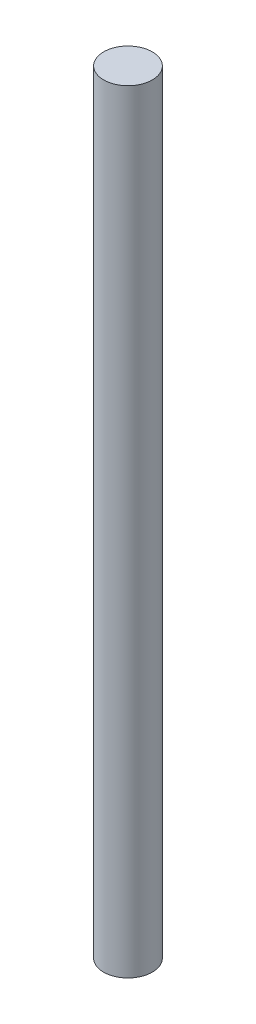
SolidWorks part; units mm, degrees
ref_plane "Front Plane" through (0, 0, 0) normal (0, 0, 1) x (1, 0, 0)
ref_plane "Top Plane" through (0, 0, 0) normal (0, 1, 0) x (1, 0, 0)
ref_plane "Right Plane" through (0, 0, 0) normal (1, 0, 0) x (0, 0, -1)
sketch "Sketch1" plane through (0, 0, 0) normal (0, 1, 0) x (1, 0, 0)
  circle A0 centre (0, 0) radius 6.3
extrude "Boss-Extrude1" add sketch "Sketch1" along normal blind 200
